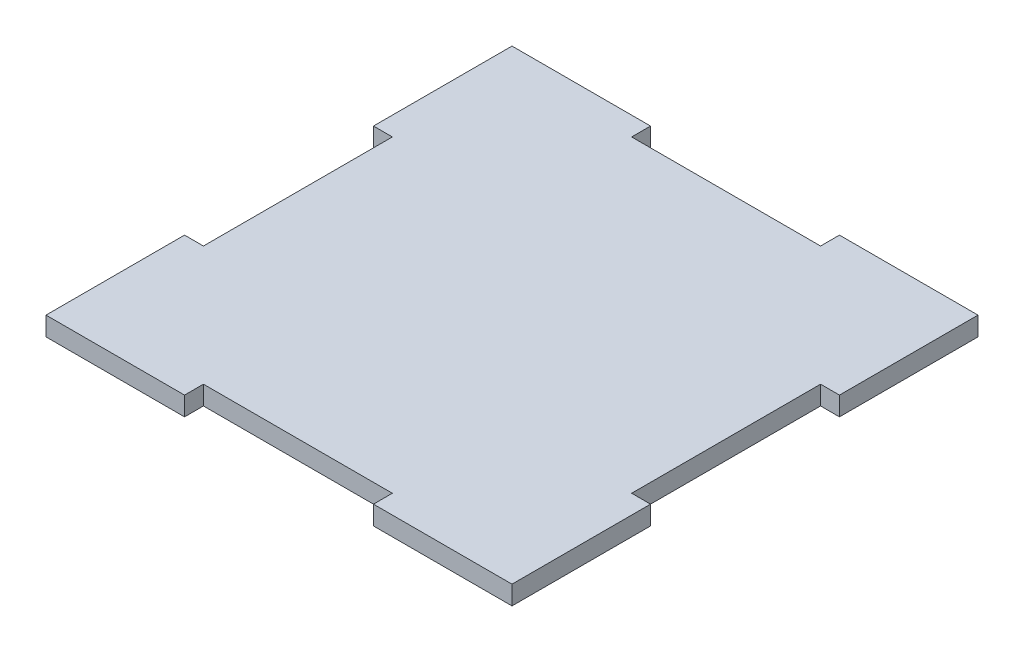
SolidWorks part; units mm, degrees
ref_plane "Plano frontal" through (0, 0, 0) normal (0, 0, 1) x (1, 0, 0)
ref_plane "Plano superior" through (0, 0, 0) normal (0, 1, 0) x (1, 0, 0)
ref_plane "Plano direito" through (0, 0, 0) normal (1, 0, 0) x (0, 0, -1)
sketch "Esboço1" plane through (0, 0, 0) normal (0, 1, 0) x (1, 0, 0)
  line L1 (-37, 37) -> (37, 37)
  line L2 (-37, 37) -> (-37, -37)
  line L3 (-37, -37) -> (37, -37)
  line L4 (37, 37) -> (37, -37)
  line L5 (-37, 37) -> (37, -37) construction
  line L6 (-37, -37) -> (37, 37) construction
  point P0 (0, 0)
  point P5 (0, 0)
  dimension "D1" = 74
  dimension "D2" = 74
extrude "Ressalto-extrusão1" add sketch "Esboço1" along normal blind 3
sketch "Esboço2" plane through (0, 3, 0) normal (0, 1, 0) x (1, 0, 0)
  line L0 (37, 37) -> (-37, 37) construction
  line L1 (-15, 37) -> (15, 37)
  line L2 (-15, 37) -> (-15, 34)
  line L3 (-15, 34) -> (15, 34)
  line L4 (15, 37) -> (15, 34)
  line L5 (37, -37) -> (37, 37) construction
  line L6 (37, 15) -> (34, 15)
  line L7 (37, 15) -> (37, -15)
  line L8 (37, -15) -> (34, -15)
  line L9 (34, 15) -> (34, -15)
  line L10 (-37, -37) -> (37, -37) construction
  line L11 (-15, -37) -> (15, -37)
  line L12 (-15, -37) -> (-15, -34)
  line L13 (-15, -34) -> (15, -34)
  line L14 (15, -37) -> (15, -34)
  line L15 (-37, 37) -> (-37, -37) construction
  line L16 (-37, 15) -> (-34, 15)
  line L17 (-37, 15) -> (-37, -15)
  line L18 (-37, -15) -> (-34, -15)
  line L19 (-34, 15) -> (-34, -15)
  point P24 (34, 0)
  point P26 (-34, 0)
  point P27 (0, 34)
  point P28 (0, -34)
  dimension "D1" = 3
  dimension "D2" = 30
extrude "Corte-extrusão1" cut sketch "Esboço2" against normal blind 3
